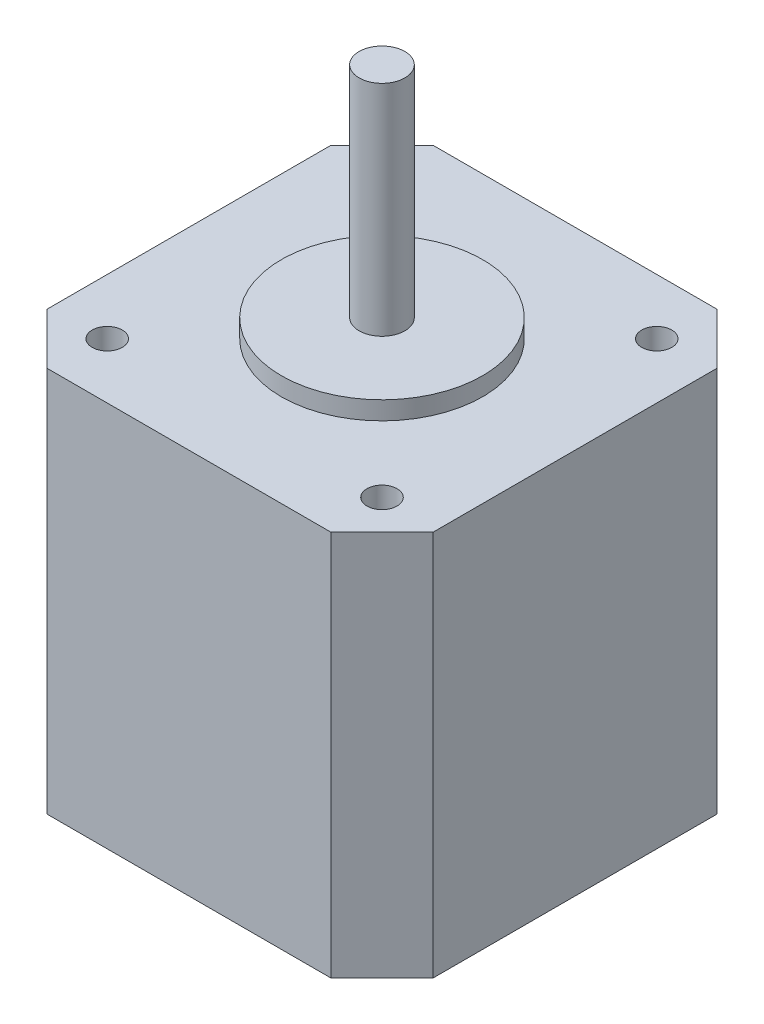
SolidWorks part; units mm, degrees
ref_plane "Plano frontal" through (0, 0, 0) normal (0, 0, 1) x (1, 0, 0)
ref_plane "Plano superior" through (0, 0, 0) normal (0, 1, 0) x (1, 0, 0)
ref_plane "Plano direito" through (0, 0, 0) normal (1, 0, 0) x (0, 0, -1)
sketch "Esboço1" plane through (0, 0, 0) normal (0, 1, 0) x (1, 0, 0)
  line L1 (-21.15, 21.15) -> (21.15, 21.15)
  line L2 (-21.15, 21.15) -> (-21.15, -21.15)
  line L3 (-21.15, -21.15) -> (21.15, -21.15)
  line L4 (21.15, 21.15) -> (21.15, -21.15)
  line L5 (-21.15, 21.15) -> (21.15, -21.15) construction
  line L6 (-21.15, -21.15) -> (21.15, 21.15) construction
  point P0 (0, 0)
  dimension "D1" = 42.3
extrude "Ressalto-extrusão1" add sketch "Esboço1" along normal mid plane 42.3
sketch "Esboço2" plane through (0, 21.15, 0) normal (0, 1, 0) x (1, 0, 0)
  circle A0 centre (0, 0) radius 11.025
  dimension "D1" = 22.05
extrude "Ressalto-extrusão2" add sketch "Esboço2" along normal blind 2
sketch "Esboço3" plane through (0, 23.15, 0) normal (0, 1, 0) x (1, 0, 0)
  circle A0 centre (0, 0) radius 2.506
  dimension "D1" = 5.012
extrude "Ressalto-extrusão3" add sketch "Esboço3" along normal blind 24
chamfer "Chanfro1" distance 5.6 angle 45 4 edges at (-21.15, 0, -21.15) (21.15, 0, -21.15) (-21.15, 0, 21.15) (21.15, 0, 21.15)
sketch "Esboço4" plane through (0, 21.15, 0) normal (0, 1, 0) x (1, 0, 0)
  line L0 (15.55, 21.15) -> (-15.55, 21.15) construction
  line L1 (-21.15, 15.55) -> (-21.15, -15.55) construction
  line L2 (21.15, -15.55) -> (21.15, 15.55) construction
  line L3 (-15.55, -21.15) -> (15.55, -21.15) construction
  circle A0 centre (-15.05, 15.05) radius 1.65
  circle A1 centre (15.05, 15.05) radius 1.65
  circle A2 centre (15.05, -15.05) radius 1.65
  circle A3 centre (-15.05, -15.05) radius 1.65
  dimension "D1" = 3.3
  dimension "D2" = 6.1
  dimension "D3" = 6.1
  dimension "D4" = 6.1
  dimension "D5" = 6.1
  dimension "D6" = 6.1
  dimension "D7" = 6.1
  dimension "D8" = 6.1
  dimension "D9" = 6.1
extrude "Corte-extrusão1" cut sketch "Esboço4" against normal blind 10
